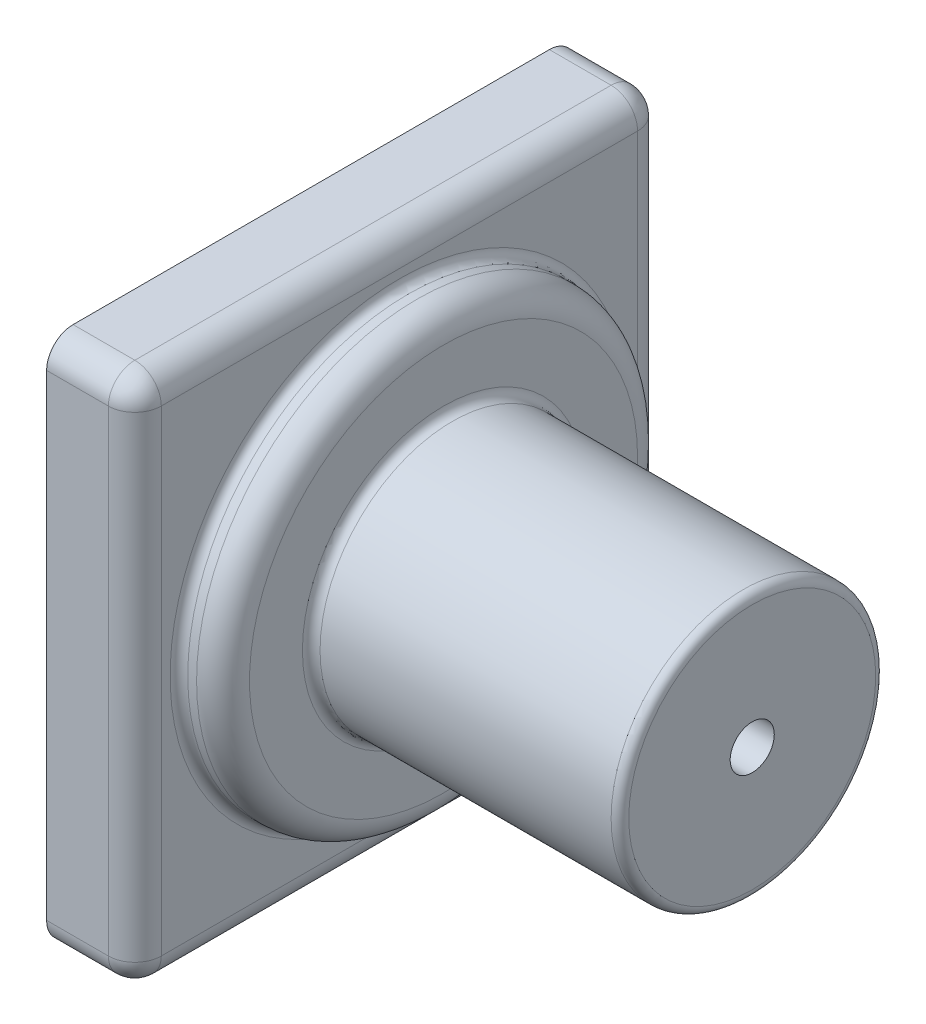
SolidWorks part; units mm, degrees
ref_plane "Front Plane" through (0, 0, 0) normal (0, 0, 1) x (1, 0, 0)
ref_plane "Top Plane" through (0, 0, 0) normal (0, 1, 0) x (1, 0, 0)
ref_plane "Right Plane" through (0, 0, 0) normal (1, 0, 0) x (0, 0, -1)
sketch "Sketch1" plane through (0, 0, 0) normal (1, 0, 0) x (0, 0, -1)
  line L1 (-30, 30) -> (30, 30)
  line L2 (-30, 30) -> (-30, -30)
  line L3 (-30, -30) -> (30, -30)
  line L4 (30, 30) -> (30, -30)
  line L5 (-30, 30) -> (30, -30) construction
  line L6 (-30, -30) -> (30, 30) construction
  point P0 (0, 0)
  dimension "D1" = 60
  dimension "D2" = 60
extrude "Boss-Extrude1" add sketch "Sketch1" along normal blind 10
sketch "Sketch2" plane through (10, 0, 0) normal (1, 0, 0) x (0, 0, -1)
  circle A0 centre (0, 0) radius 25
  dimension "D1" = 50
extrude "Boss-Extrude2" add sketch "Sketch2" along normal blind 5
sketch "Sketch3" plane through (15, 0, 0) normal (1, 0, 0) x (0, 0, -1)
  circle A0 centre (0, 0) radius 15
  dimension "D1" = 30
extrude "Boss-Extrude3" add sketch "Sketch3" along normal blind 35
sketch "Sketch4" plane through (50, 0, 0) normal (1, 0, 0) x (0, 0, -1)
  circle A0 centre (0, 0) radius 2.5
  dimension "D1" = 5
extrude "Cut-Extrude1" cut sketch "Sketch4" against normal blind 5
fillet "Fillet1" radius 3 8 edges at (5, 30, -30) (5, -30, -30) (10, 0, -30) (10, -30, 0) (5, -30, 30) (10, 0, 30) (10, 30, 0) (5, 30, 30)
fillet "Fillet2" radius 3 1 edges at (15, 0, -25)
fillet "Fillet3" radius 1 3 edges at (50, 0, -15) (15, 0, -15) (10, 0, -25)
